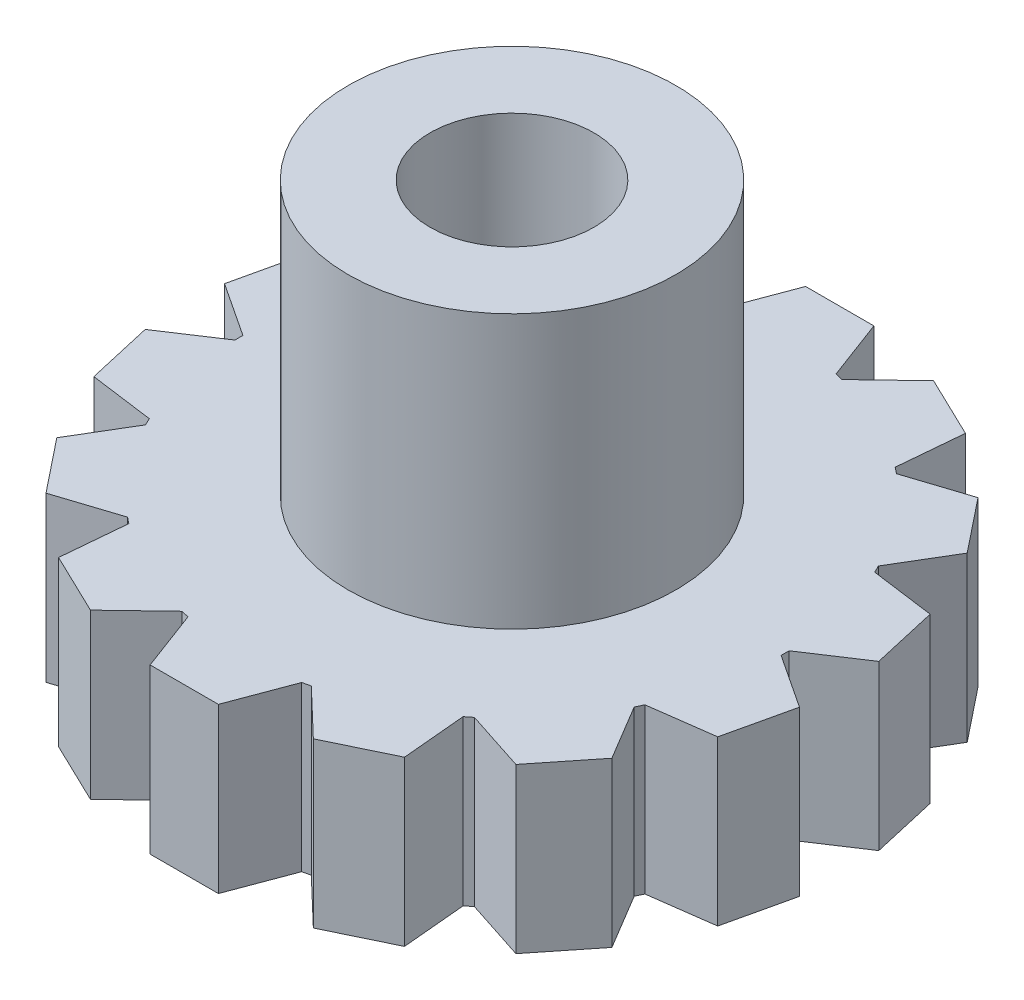
SolidWorks part; units mm, degrees
ref_plane "Front Plane" through (0, 0, 0) normal (0, 0, 1) x (1, 0, 0)
ref_plane "Top Plane" through (0, 0, 0) normal (0, 1, 0) x (1, 0, 0)
ref_plane "Right Plane" through (0, 0, 0) normal (1, 0, 0) x (0, 0, -1)
sketch "Sketch1" plane through (0, 0, 0) normal (0, 1, 0) x (1, 0, 0)
  circle A0 centre (0, 0) radius 3.15
  circle A1 centre (0, 0) radius 10
  dimension "D1" = 6.3
  dimension "D2" = 20
extrude "Boss-Extrude1" add sketch "Sketch1" along normal blind 6
sketch "Sketch2" plane through (0, 6, 0) normal (0, 1, 0) x (1, 0, 0)
  circle A0 centre (0, 0) radius 3
  circle A1 centre (0, 0) radius 6
  dimension "D1" = 12
extrude "Boss-Extrude2" add sketch "Sketch2" along normal blind 10
sketch "Sketch3" plane through (0, 6, 0) normal (0, 1, 0) x (1, 0, 0)
  line L0 (0, 0) -> (0, 10) construction
  line L1 (-2, 10) -> (2, 10) construction
  line L2 (0, 10) -> (0, 12) construction
  line L3 (-1.25, 12) -> (1.25, 12)
  line L4 (1.25, 12) -> (2, 10)
  line L5 (2, 10) -> (2.0822, 9.7808)
  line L6 (-1.25, 12) -> (-2, 10)
  line L7 (-2, 10) -> (-2.0822, 9.7808)
  line L8 (-2, 0) -> (2, 0)
  line L9 (2.5369, 9.8775) -> (2.3677, 9.7156)
  line L10 (4.0804, 11.354) -> (2.5369, 9.8775)
  line L11 (4.0804, 11.354) -> (6.3328, 10.2693)
  line L12 (6.3328, 10.2693) -> (6.1408, 8.1419)
  line L13 (6.1408, 8.1419) -> (6.1197, 7.9088)
  line L14 (6.5713, 7.7986) -> (6.3487, 7.7262)
  line L15 (8.6026, 8.4592) -> (6.5713, 7.7986)
  line L16 (8.6026, 8.4592) -> (10.1613, 6.5046)
  line L17 (10.1613, 6.5046) -> (9.0653, 4.6712)
  line L18 (9.0653, 4.6712) -> (8.9452, 4.4703)
  line L19 (9.3042, 4.1751) -> (9.0723, 4.2064)
  line L20 (11.421, 3.8889) -> (9.3042, 4.1751)
  line L21 (11.421, 3.8889) -> (11.9773, 1.4516)
  line L22 (11.9773, 1.4516) -> (10.1943, 0.2754)
  line L23 (10.1943, 0.2754) -> (9.9989, 0.1465)
  line L24 (10.1943, -0.2754) -> (9.9989, -0.1465)
  line L25 (11.9773, -1.4516) -> (10.1943, -0.2754)
  line L26 (11.9773, -1.4516) -> (11.421, -3.8889)
  line L27 (11.421, -3.8889) -> (9.3042, -4.1751)
  line L28 (9.3042, -4.1751) -> (9.0723, -4.2064)
  line L29 (9.0653, -4.6712) -> (8.9452, -4.4703)
  line L30 (10.1613, -6.5046) -> (9.0653, -4.6712)
  line L31 (10.1613, -6.5046) -> (8.6026, -8.4592)
  line L32 (8.6026, -8.4592) -> (6.5713, -7.7986)
  line L33 (6.5713, -7.7986) -> (6.3487, -7.7262)
  line L34 (6.1408, -8.1419) -> (6.1197, -7.9088)
  line L35 (6.3328, -10.2693) -> (6.1408, -8.1419)
  line L36 (6.3328, -10.2693) -> (4.0804, -11.354)
  line L37 (4.0804, -11.354) -> (2.5369, -9.8775)
  line L38 (2.5369, -9.8775) -> (2.3677, -9.7156)
  line L39 (2, -10) -> (2.0822, -9.7808)
  line L40 (1.25, -12) -> (2, -10)
  line L41 (1.25, -12) -> (-1.25, -12)
  line L42 (-1.25, -12) -> (-2, -10)
  line L43 (-2, -10) -> (-2.0822, -9.7808)
  line L44 (-2.5369, -9.8775) -> (-2.3677, -9.7156)
  line L45 (-4.0804, -11.354) -> (-2.5369, -9.8775)
  line L46 (-4.0804, -11.354) -> (-6.3328, -10.2693)
  line L47 (-6.3328, -10.2693) -> (-6.1408, -8.1419)
  line L48 (-6.1408, -8.1419) -> (-6.1197, -7.9088)
  line L49 (-6.5713, -7.7986) -> (-6.3487, -7.7262)
  line L50 (-8.6026, -8.4592) -> (-6.5713, -7.7986)
  line L51 (-8.6026, -8.4592) -> (-10.1613, -6.5046)
  line L52 (-10.1613, -6.5046) -> (-9.0653, -4.6712)
  line L53 (-9.0653, -4.6712) -> (-8.9452, -4.4703)
  line L54 (-9.3042, -4.1751) -> (-9.0723, -4.2064)
  line L55 (-11.421, -3.8889) -> (-9.3042, -4.1751)
  line L56 (-11.421, -3.8889) -> (-11.9773, -1.4516)
  line L57 (-11.9773, -1.4516) -> (-10.1943, -0.2754)
  line L58 (-10.1943, -0.2754) -> (-9.9989, -0.1465)
  line L59 (-10.1943, 0.2754) -> (-9.9989, 0.1465)
  line L60 (-11.9773, 1.4516) -> (-10.1943, 0.2754)
  line L61 (-11.9773, 1.4516) -> (-11.421, 3.8889)
  line L62 (-11.421, 3.8889) -> (-9.3042, 4.1751)
  line L63 (-9.3042, 4.1751) -> (-9.0723, 4.2064)
  line L64 (-9.0653, 4.6712) -> (-8.9452, 4.4703)
  line L65 (-10.1613, 6.5046) -> (-9.0653, 4.6712)
  line L66 (-10.1613, 6.5046) -> (-8.6026, 8.4592)
  line L67 (-8.6026, 8.4592) -> (-6.5713, 7.7986)
  line L68 (-6.5713, 7.7986) -> (-6.3487, 7.7262)
  line L69 (-6.1408, 8.1419) -> (-6.1197, 7.9088)
  line L70 (-6.3328, 10.2693) -> (-6.1408, 8.1419)
  line L71 (-6.3328, 10.2693) -> (-4.0804, 11.354)
  line L72 (-4.0804, 11.354) -> (-2.5369, 9.8775)
  line L73 (-2.5369, 9.8775) -> (-2.3677, 9.7156)
  circle A0 centre (0, 0) radius 10 construction
  arc A1 (6.1197, 7.9088) -> (2.3677, 9.7156) centre (0, 0) ccw
  arc A2 (8.9452, 4.4703) -> (6.3487, 7.7262) centre (0, 0) ccw
  circle A3 centre (0, 0) radius 10
  arc A4 (2.0822, 9.7808) -> (-2.0822, 9.7808) centre (0, 0) ccw
  arc A5 (9.9989, 0.1465) -> (9.0723, 4.2064) centre (0, 0) ccw
  arc A6 (9.0723, -4.2064) -> (9.9989, -0.1465) centre (0, 0) ccw
  arc A7 (6.3487, -7.7262) -> (8.9452, -4.4703) centre (0, 0) ccw
  arc A8 (2.3677, -9.7156) -> (6.1197, -7.9088) centre (0, 0) ccw
  arc A9 (-2.0822, -9.7808) -> (2.0822, -9.7808) centre (0, 0) ccw
  arc A10 (-6.1197, -7.9088) -> (-2.3677, -9.7156) centre (0, 0) ccw
  arc A11 (-8.9452, -4.4703) -> (-6.3487, -7.7262) centre (0, 0) ccw
  arc A12 (-9.9989, -0.1465) -> (-9.0723, -4.2064) centre (0, 0) ccw
  arc A13 (-9.0723, 4.2064) -> (-9.9989, 0.1465) centre (0, 0) ccw
  arc A14 (-6.3487, 7.7262) -> (-8.9452, 4.4703) centre (0, 0) ccw
  arc A15 (-2.3677, 9.7156) -> (-6.1197, 7.9088) centre (0, 0) ccw
  point P9 (0, 10)
  point P13 (0, 12)
  point P99 (0, 0)
  circle M21 centre (0, 0) radius 10
  dimension "D1" = 4
  dimension "D2" = 2
  dimension "D3" = 2.5
  dimension "D4" = 10
  dimension "D5" = 0
  dimension "D6" = 14
extrude "Boss-Extrude3" add sketch "Sketch3" against normal up to surface (6 mm away) contours L6 L7 L5 L4 L3 M21 | L73 L72 L71 L70 L69 M21 | L68 L67 L66 L65 L64 M21 | L63 L62 L61 L60 L59 M21 | L58 L57 L56 L55 L54 M21 | L53 L52 L51 L50 L49 M21 | L43 L42 L41 L40 L39 M21 | L48 L47 L46 L45 L44 M21 | L38 L37 L36 L35 L34 M21 | L33 L32 L31 L30 L29 M21 | L28 L27 L26 L25 L24 M21 | L23 L22 L21 L20 L19 M21 | L18 L17 L16 L15 L14 M21 | L13 L12 L11 L10 L9 M21 up to face at (0, 0, 10)
